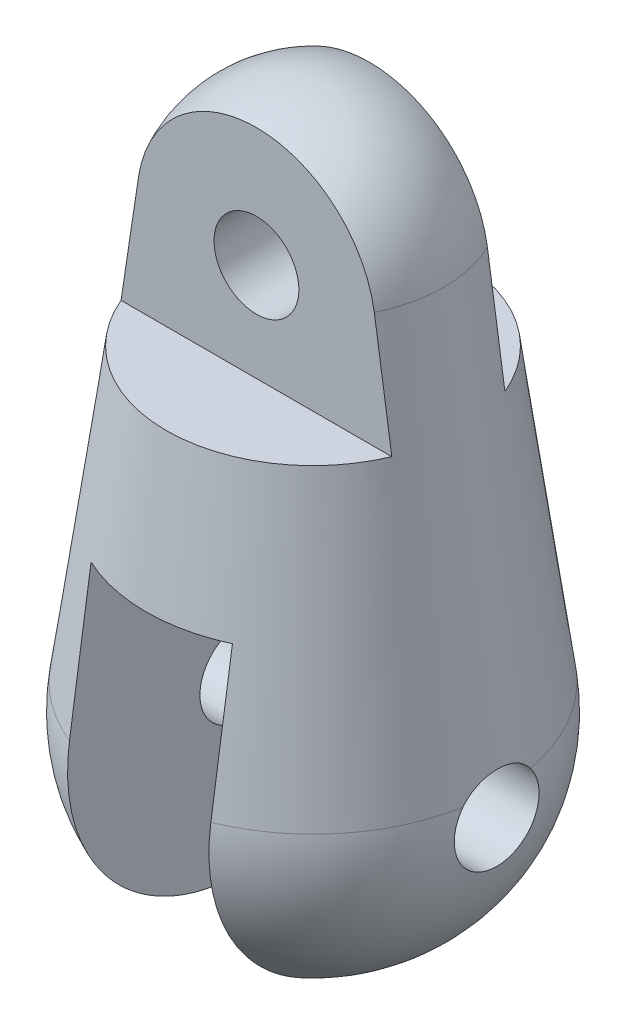
SolidWorks part; units mm, degrees
ref_plane "Front Plane" through (0, 0, 0) normal (0, 0, 1) x (1, 0, 0)
ref_plane "Top Plane" through (0, 0, 0) normal (0, 1, 0) x (1, 0, 0)
ref_plane "Right Plane" through (0, 0, 0) normal (1, 0, 0) x (0, 0, -1)
sketch "Sketch1" plane through (0, 0, 0) normal (0, 0, 1) x (1, 0, 0)
  line L1 (-13.8692, 45.9091) -> (-19.8132, 2.7273)
  line L6 (0, 58) -> (0, -20)
  arc A1 (0, 58) -> (-13.8692, 45.9091) centre (0, 44) ccw
  arc A3 (-19.8132, 2.7273) -> (-7.5, -18.5405) centre (0, 0) ccw
  arc A4 (-19.8132, 2.7273) -> (-7.5, -18.5405) centre (0, 0) ccw
  arc A5 (-19.8132, 2.7273) -> (0, -20) centre (0, 0) ccw
  arc A8 (-19.8132, 2.7273) -> (0, -20) centre (0, 0) ccw
  dimension "D2" = 28
  dimension "D1" = 44
  dimension "D5" = 44
revolve "Revolve1" add sketch "Sketch1" angle 360 about L6
sketch "Sketch6" plane through (0, 0, 0) normal (0, 0, 1) x (1, 0, 0)
  line L1 (7.5, -20) -> (7.5, 18)
  line L2 (7.5, 18) -> (-7.5, 18)
  line L4 (-7.5, -20) -> (7.5, -20)
  line L5 (-7.5, -20) -> (-7.5, 18)
  dimension "D2" = 38
extrude "Cut-Extrude3" cut sketch "Sketch6" against normal through all both and the other way through all contours L1 L2 L5 L4
sketch "Sketch10" plane through (0, 0, 0) normal (1, 0, 0) x (0, 0, -1)
  line L2 (6, 33.5908) -> (6, 56.8336)
  line L3 (6, 33.5908) -> (23.3807, 33.5908)
  line L4 (-6, 33.5908) -> (-6, 56.8336)
  line L5 (-6, 33.5908) -> (-23.3807, 33.5908)
  line L6 (6, 56.8336) -> (23.3807, 56.8336)
  line L7 (23.3807, 56.8336) -> (23.3807, 33.5908)
  line L8 (-6, 56.8336) -> (-23.3807, 56.8336)
  line L9 (-23.3807, 56.8336) -> (-23.3807, 33.5908)
extrude "Cut-Extrude4" cut sketch "Sketch10" against normal through all both and the other way through all contours L8 L9 L5 L4 | L6 L7 L3 L2
sketch "Sketch11" plane through (0, 0, -6) normal (0, 0, -1) x (-1, 0, 0)
  circle A0 centre (0, 44) radius 4.5
  dimension "D2" = 9
extrude "Cut-Extrude5" cut sketch "Sketch11" against normal through all both and the other way through all
sketch "Sketch12" plane through (0, 0, 0) normal (1, 0, 0) x (0, 0, -1)
  circle A0 centre (0, 0) radius 4.5
  dimension "D1" = 9
extrude "Cut-Extrude6" cut sketch "Sketch12" against normal through all both and the other way through all
